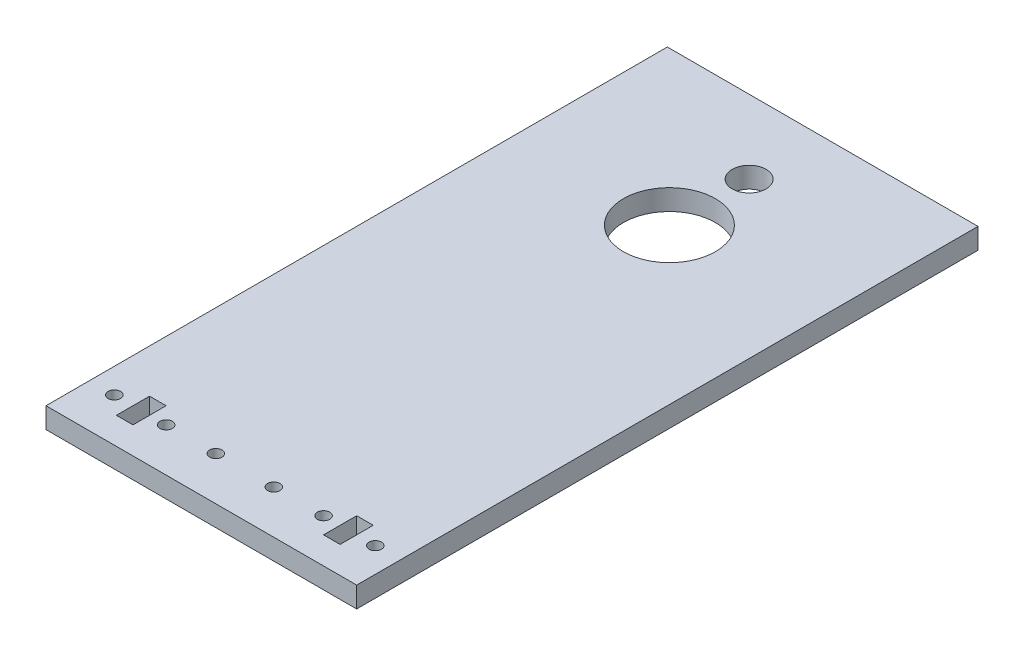
SolidWorks part; units mm, degrees
ref_plane "前视基准面" through (0, 0, 0) normal (0, 0, 1) x (1, 0, 0)
ref_plane "上视基准面" through (0, 0, 0) normal (0, 1, 0) x (1, 0, 0)
ref_plane "右视基准面" through (0, 0, 0) normal (1, 0, 0) x (0, 0, -1)
sketch "草图1" plane through (0, 0, 0) normal (0, 1, 0) x (1, 0, 0)
  line L0 (0, 0) -> (75, 0)
  line L1 (75, 0) -> (75, 150)
  line L2 (75, 150) -> (0, 150)
  line L3 (0, 150) -> (0, 0)
  line L4 (75, 0) -> (75, 11)
  line L6 (75, 8.5) -> (75, 10)
  line L12 (75, 0) -> (64.5, 0)
  line L14 (10.5, 6.5) -> (10.5, 10.5)
  line L15 (12.5, 6.5) -> (10.5, 6.5)
  line L18 (37.5, 11) -> (37.5, 0)
  line L24 (37.5, 150) -> (37.5, 113)
  line L25 (37.5, 113) -> (37.5, 93.75)
  line L26 (12.5, 14.5) -> (14.5, 14.5)
  line L27 (14.5, 14.5) -> (14.5, 6.5)
  line L28 (14.5, 6.5) -> (12.5, 6.5)
  line L40 (10.5, 10) -> (10.5, 12.5)
  line L42 (75, 10) -> (75, 10.5)
  line L43 (75, 10.5) -> (69, 10.5)
  line L44 (69, 10.5) -> (64.5, 10.5)
  line L45 (64.5, 10.5) -> (62.5, 10.5)
  line L46 (62.5, 10.5) -> (56.5, 10.5)
  line L47 (56.5, 10.5) -> (44.5, 10.5)
  line L48 (44.5, 10.5) -> (37.5, 10.5)
  line L49 (64.5, 10.5) -> (64.5, 14.5)
  line L50 (64.5, 14.5) -> (62.5, 14.5)
  line L51 (62.5, 14.5) -> (62.5, 10.5)
  line L52 (62.5, 10.5) -> (62.5, 6.5)
  line L53 (62.5, 6.5) -> (64.5, 6.5)
  line L54 (64.5, 6.5) -> (64.5, 10.5)
  line L55 (55.0858, 10) -> (56.5, 10)
  line L56 (12.5, 10.5) -> (12.5, 6.5)
  line L57 (12.5, 14.5) -> (12.5, 10.5)
  line L58 (10.5, 14.5) -> (12.5, 14.5)
  line L59 (10.5, 10.5) -> (10.5, 14.5)
  line L60 (37.5, 10.5) -> (75, 10.5)
  line L61 (75, 10.5) -> (75, 0)
  line L62 (37.5, 0) -> (75, 0)
  line L63 (62.5, 14.5) -> (60.5, 14.5)
  line L64 (60.5, 14.5) -> (60.5, 6.5)
  line L65 (60.5, 6.5) -> (62.5, 6.5)
  circle A6 centre (37.5, 113) radius 11.1
  circle A7 centre (37.5, 113) radius 19.25
  arc A8 (39.6873, 150) -> (35.3127, 150) centre (37.5, 113) ccw
  arc A11 (37.5, 150.0646) -> (39.6873, 150) centre (37.5, 113) cw
  circle A26 centre (69, 10.5) radius 1.5
  circle A27 centre (56.5, 10.5) radius 1.5
  circle A28 centre (44.5, 10.5) radius 1.5
  circle A29 centre (30.5, 10.5) radius 1.5
  circle A30 centre (18.5, 10.5) radius 1.5
  circle A31 centre (6, 10.5) radius 1.5
  circle A32 centre (37.5, 132.25) radius 4.1
  dimension "D1" = 8.5
  dimension "D2" = 37
extrude "凸台-拉伸6" add sketch "草图1" along normal blind 5
